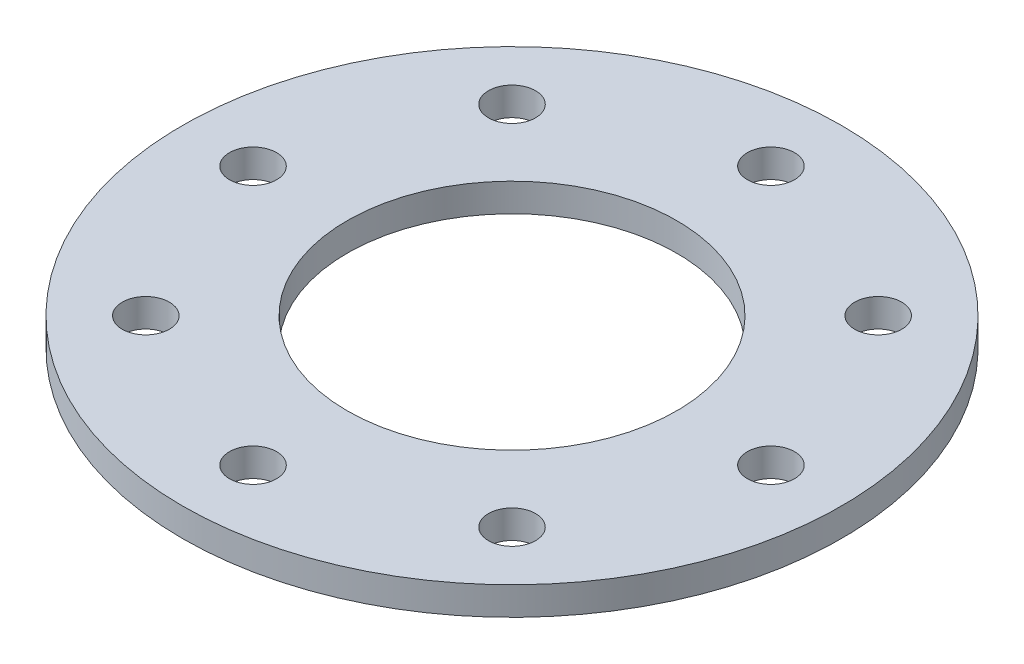
SolidWorks part; units mm, degrees
ref_plane "Front Plane" through (0, 0, 0) normal (0, 0, 1) x (1, 0, 0)
ref_plane "Top Plane" through (0, 0, 0) normal (0, 1, 0) x (1, 0, 0)
ref_plane "Right Plane" through (0, 0, 0) normal (1, 0, 0) x (0, 0, -1)
sketch "Sketch1" plane through (0, 0, 0) normal (0, 1, 0) x (1, 0, 0)
  line L0 (0, 0) -> (26.2939, 0) construction
  line L1 (0, 0) -> (0, 23.8813) construction
  circle A0 centre (0, 0) radius 14
  circle A2 centre (0, 0) radius 7
  dimension "D1" = 28
  dimension "D2" = 14
extrude "Boss-Extrude1" add sketch "Sketch1" along normal mid plane 1.2
sketch "Sketch2" plane through (0, 0.6, 0) normal (0, 1, 0) x (1, 0, 0)
  point P0 (0, 11)
  dimension "D1" = 11
hole_wizard "Ø2.0mm Dowel Hole1" positions "Sketch3" profile "Sketch4" hole size "Ø2.0" standard "ANSI Metric" end condition through all
sketch "Sketch3" plane through (0, 0.6, 0) normal (0, 1, 0) x (1, 0, 0)
  point P0 (0, 11)
sketch "Sketch4" plane through (0, 0.6, -11) normal (1, 0, 0) x (0, 0, 1)
  line L0 (0, 0) -> (0, 1.2)
  line L1 (0, 1.2) -> (1, 1.2)
  line L2 (1, 1.2) -> (1, 0)
  line L5 (1, 0) -> (0, 0)
  line L11 (0, -6.35) -> (0, 107.95) construction
  dimension "Thru Hole Dia." = 2
  dimension "Thru Hole Depth" = 1.2
pattern_circular "CirPattern1" count 8 over 360 about axis through (0, 0, 0) along (0, 1, 0) of "Ø2.0mm Dowel Hole1"
